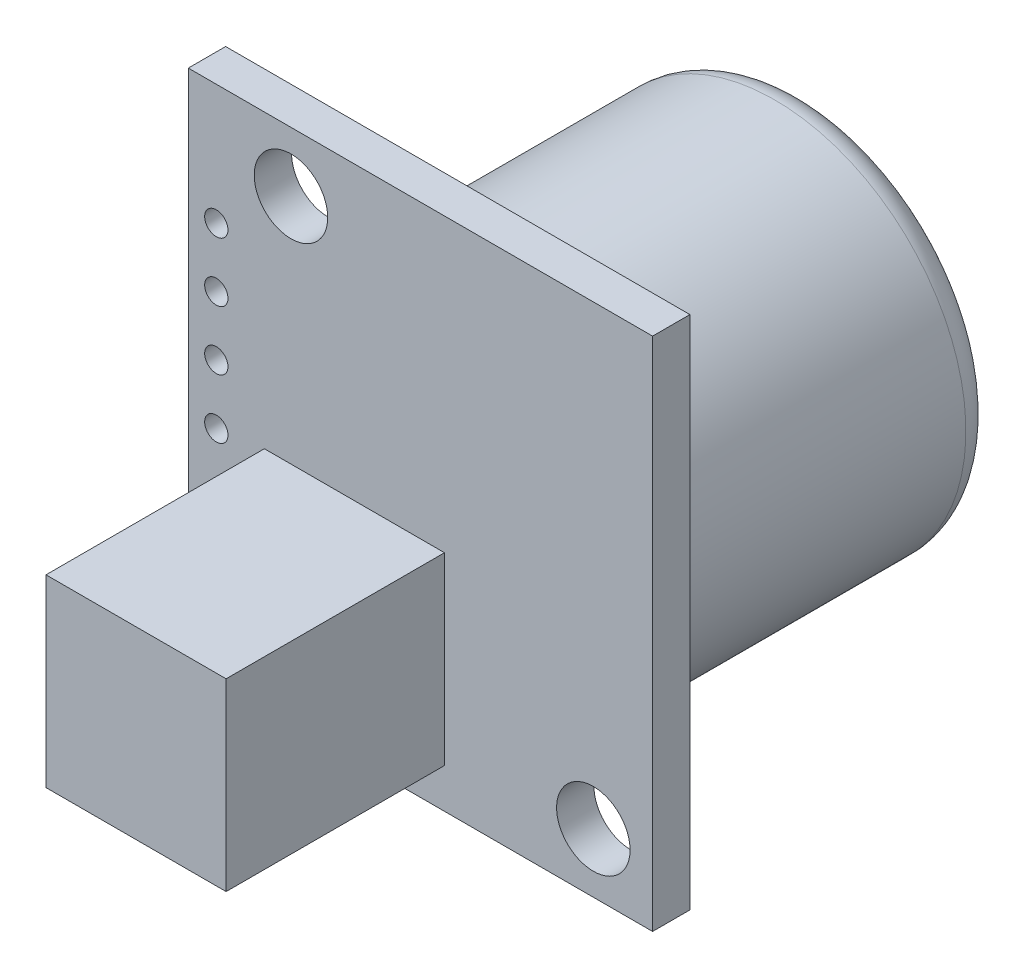
SolidWorks part; units mm, degrees
material "ABS"
ref_plane "Front Plane" through (0, 0, 0) normal (0, 0, 1) x (1, 0, 0)
ref_plane "Top Plane" through (0, 0, 0) normal (0, 1, 0) x (1, 0, 0)
ref_plane "Right Plane" through (0, 0, 0) normal (1, 0, 0) x (0, 0, -1)
sketch "Sketch1" plane through (0, 0, 0) normal (0, 0, 1) x (1, 0, 0)
  line L1 (-9.95, -11.05) -> (9.95, -11.05)
  line L2 (-9.95, -11.05) -> (-9.95, 11.05)
  line L3 (-9.95, 11.05) -> (9.95, 11.05)
  line L4 (9.95, -11.05) -> (9.95, 11.05)
  line L5 (-9.95, -11.05) -> (9.95, 11.05) construction
  line L6 (-9.95, 11.05) -> (9.95, -11.05) construction
  circle A0 centre (-5.55, 8.49) radius 1.5748
  circle A1 centre (7.41, -8.51) radius 1.5748
  circle A2 centre (-8.75, -9.35) radius 0.5
  circle A3 centre (-8.75, -6.81) radius 0.5
  circle A4 centre (-8.75, -4.27) radius 0.5
  circle A5 centre (-8.75, -1.73) radius 0.5
  circle A6 centre (-8.75, 0.81) radius 0.5
  circle A7 centre (-8.75, 3.35) radius 0.5
  circle A8 centre (-8.75, 5.89) radius 0.5
  point P0 (0, 0)
  dimension "D7" = 3.1496
  dimension "D10" = 1
  dimension "D11" = 7
  dimension "D1" = 22.1
  dimension "D2" = 19.9
  dimension "D3" = 15.5
  dimension "D4" = 17
  dimension "D5" = 2.54
  dimension "D6" = 2.54
  dimension "D8" = 1.7
  dimension "D9" = 18.7
  dimension "D12" = 0.81
extrude "Boss-Extrude1" add sketch "Sketch1" along normal blind 1.6
sketch "Sketch2" plane through (0, 0, 0) normal (0, 0, -1) x (-1, 0, 0)
  line L0 (-7.41, -8.51) -> (5.55, 8.49) construction
  circle A0 centre (-0.93, -0.01) radius 8.2
  dimension "D1" = 16.4
extrude "Boss-Extrude2" add sketch "Sketch2" along normal blind 13.9192
fillet "Fillet2" radius 1.27 1 edges at (-7.27, -0.01, -13.9192)
sketch "Sketch3" plane through (0, 0, 1.6) normal (0, 0, 1) x (1, 0, 0)
  line L0 (9.95, 11.05) -> (-9.95, 11.05) construction
  line L1 (-6.69, -9.35) -> (1.03, -9.35)
  line L2 (-6.69, -9.35) -> (-6.69, -1.45)
  line L3 (-6.69, -1.45) -> (1.03, -1.45)
  line L4 (1.03, -9.35) -> (1.03, -1.45)
  line L5 (-9.95, -11.05) -> (9.95, -11.05) construction
  line L6 (9.95, -11.05) -> (9.95, 11.05) construction
  dimension "D1" = 12.5
  dimension "D2" = 7.72
  dimension "D3" = 1.7
  dimension "D4" = 8.92
extrude "Boss-Extrude3" add sketch "Sketch3" along normal blind 9.36
